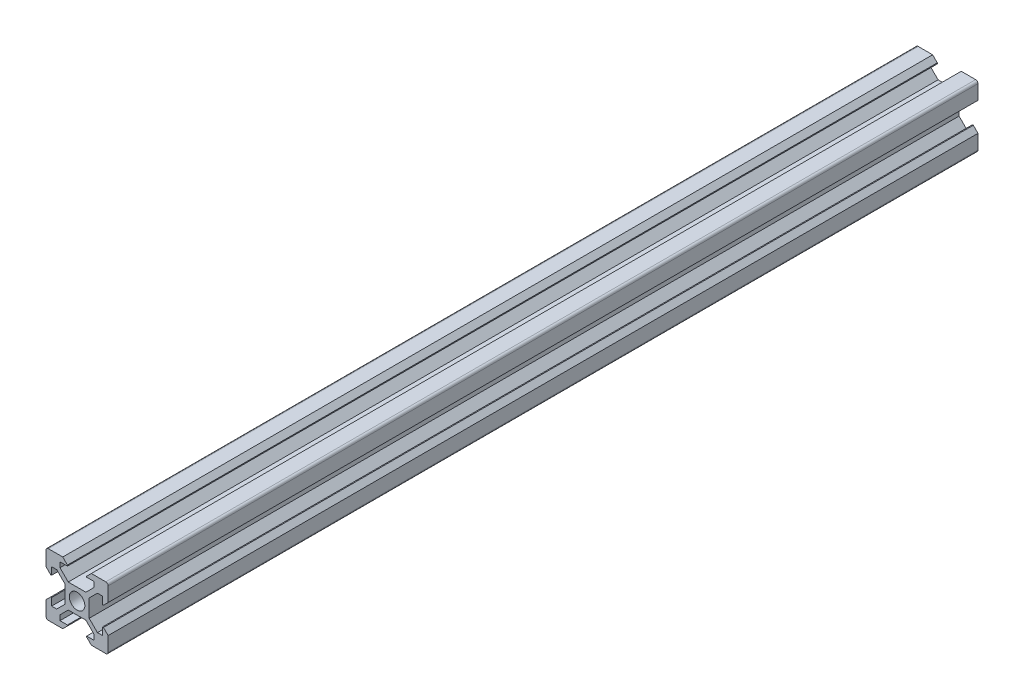
SolidWorks part; units mm, degrees
other "Markup1"
sketch "Sketch1" plane through (10, 10, 480) normal (0.5774, 0.5773, 0.5774) x (0.7071, 0, -0.7071)
ref_plane "Alzado" through (0, 0, 0) normal (0, 0, 1) x (1, 0, 0)
ref_plane "Planta" through (0, 0, 0) normal (0, 1, 0) x (1, 0, 0)
ref_plane "Vista lateral" through (0, 0, 0) normal (1, 0, 0) x (0, 0, -1)
sketch "Croquis1" plane through (0, 0, 0) normal (0, 0, 1) x (1, 0, 0)
  line L0 (-4.6, 10) -> (-3.1, 8.5)
  line L3 (-4.6, 10) -> (-9.25, 10)
  line L5 (-3.1, 8.5) -> (-3.1, 8.2)
  line L6 (-3.1, 8.2) -> (-5.5, 8.2)
  line L7 (-5.5, 8.2) -> (-5.5, 6.5607)
  line L8 (-5.5, 6.5607) -> (-2.84, 3.9007)
  line L9 (-2.84, 3.9007) -> (0, 3.9007)
  line L10 (0, 0) -> (-15.3499, 15.3499) construction
  line L11 (-3.9007, 2.84) -> (-3.9007, 0)
  line L12 (-6.5607, 5.5) -> (-3.9007, 2.84)
  line L13 (-8.2, 5.5) -> (-6.5607, 5.5)
  line L14 (-8.2, 3.1) -> (-8.2, 5.5)
  line L15 (-8.5, 3.1) -> (-8.2, 3.1)
  line L16 (-10, 4.6) -> (-10, 9.25)
  line L17 (-10, 4.6) -> (-8.5, 3.1)
  line L18 (10, 4.6) -> (8.5, 3.1)
  line L19 (10, 4.6) -> (10, 9.25)
  line L20 (8.5, 3.1) -> (8.2, 3.1)
  line L21 (8.2, 3.1) -> (8.2, 5.5)
  line L22 (8.2, 5.5) -> (6.5607, 5.5)
  line L23 (6.5607, 5.5) -> (3.9007, 2.84)
  line L24 (3.9007, 2.84) -> (3.9007, 0)
  line L25 (5.5, 6.5607) -> (2.84, 3.9007)
  line L26 (5.5, 8.2) -> (5.5, 6.5607)
  line L27 (3.1, 8.2) -> (5.5, 8.2)
  line L28 (3.1, 8.5) -> (3.1, 8.2)
  line L29 (4.6, 10) -> (9.25, 10)
  line L30 (4.6, 10) -> (3.1, 8.5)
  line L31 (2.84, 3.9007) -> (0, 3.9007)
  line L32 (4.6, -10) -> (3.1, -8.5)
  line L33 (4.6, -10) -> (9.25, -10)
  line L34 (3.1, -8.5) -> (3.1, -8.2)
  line L35 (3.1, -8.2) -> (5.5, -8.2)
  line L36 (5.5, -8.2) -> (5.5, -6.5607)
  line L37 (5.5, -6.5607) -> (2.84, -3.9007)
  line L38 (2.84, -3.9007) -> (0, -3.9007)
  line L39 (6.5607, -5.5) -> (3.9007, -2.84)
  line L40 (8.2, -5.5) -> (6.5607, -5.5)
  line L41 (8.2, -3.1) -> (8.2, -5.5)
  line L42 (8.5, -3.1) -> (8.2, -3.1)
  line L43 (10, -4.6) -> (10, -9.25)
  line L44 (10, -4.6) -> (8.5, -3.1)
  line L45 (3.9007, -2.84) -> (3.9007, 0)
  line L46 (-10, -4.6) -> (-8.5, -3.1)
  line L47 (-10, -4.6) -> (-10, -9.25)
  line L48 (-8.5, -3.1) -> (-8.2, -3.1)
  line L49 (-8.2, -3.1) -> (-8.2, -5.5)
  line L50 (-8.2, -5.5) -> (-6.5607, -5.5)
  line L51 (-6.5607, -5.5) -> (-3.9007, -2.84)
  line L52 (-3.9007, -2.84) -> (-3.9007, 0)
  line L53 (-5.5, -6.5607) -> (-2.84, -3.9007)
  line L54 (-5.5, -8.2) -> (-5.5, -6.5607)
  line L55 (-3.1, -8.2) -> (-5.5, -8.2)
  line L56 (-3.1, -8.5) -> (-3.1, -8.2)
  line L57 (-4.6, -10) -> (-9.25, -10)
  line L58 (-4.6, -10) -> (-3.1, -8.5)
  line L59 (-2.84, -3.9007) -> (0, -3.9007)
  circle A0 centre (0, 0) radius 2.5
  arc A1 (-9.25, 10) -> (-10, 9.25) centre (-9.25, 9.25) ccw
  arc A2 (10, 9.25) -> (9.25, 10) centre (9.25, 9.25) ccw
  arc A3 (9.25, -10) -> (10, -9.25) centre (9.25, -9.25) ccw
  arc A4 (-10, -9.25) -> (-9.25, -10) centre (-9.25, -9.25) ccw
  point P18 (-10, 10)
  point P37 (10, 10)
  point P55 (10, -10)
  point P73 (-10, -10)
  point P79 (0, 0)
  dimension "D1" = 5
  dimension "D5" = 0.75
  dimension "D2" = 10
  dimension "D3" = 10
  dimension "D4" = 4.6
  dimension "D6" = 5.5
  dimension "D7" = 135
  dimension "D8" = 0.75
  dimension "D9" = 225
  dimension "D10" = 2.84
  dimension "D11" = 1.8
  dimension "D12" = 3.1
  dimension "D13" = 4
extrude "Saliente-Extruir1" add sketch "Croquis1" along normal blind 326
sketch "Sketch2" plane through (0, 0, 0) normal (0, 1, 0) x (1, 0, 0)
  line L0 (-4.6, 0) -> (-9.25, 0) construction
  line L1 (-57.4359, -280) -> (82.1467, -280)
  line L2 (-57.4359, -280) -> (-57.4359, -522.4329)
  line L3 (-57.4359, -522.4329) -> (82.1467, -522.4329)
  line L4 (82.1467, -280) -> (82.1467, -522.4329)
  dimension "D1" = 280
extrude "Cut-Extrude1" cut sketch "Sketch2" against normal blind 30 and the other way blind 47
